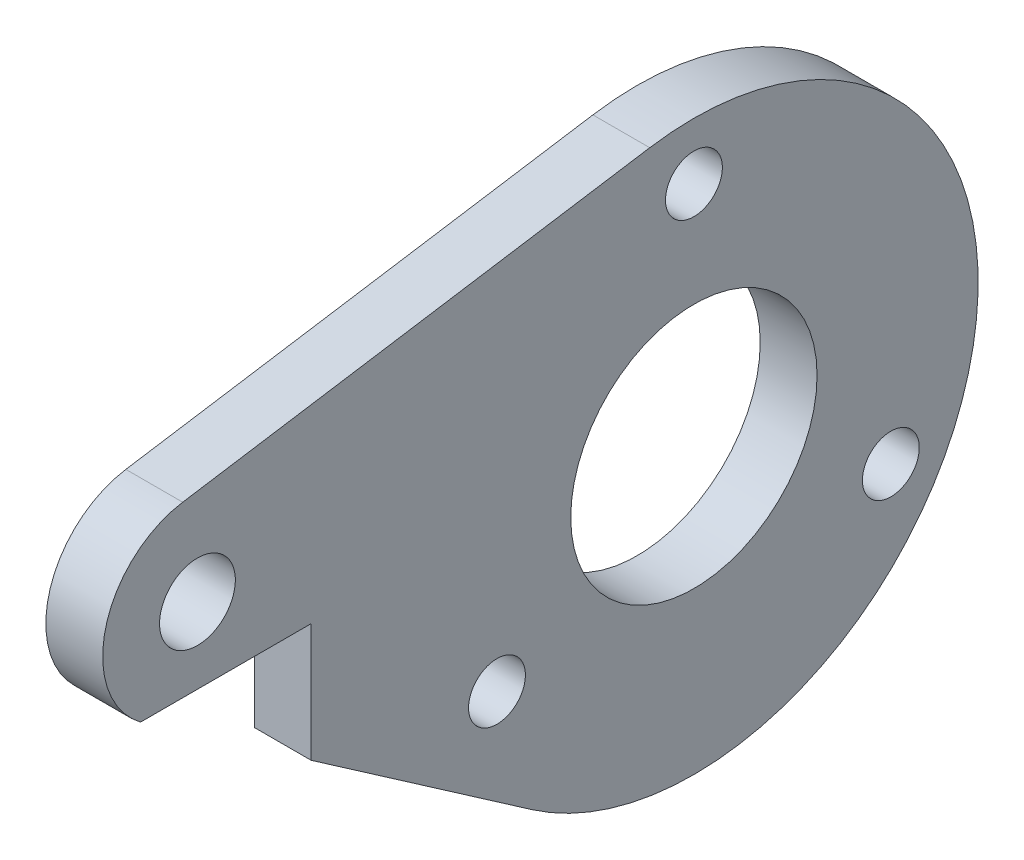
SolidWorks part; units mm, degrees
ref_plane "Plan de face" through (0, 0, 0) normal (0, 0, 1) x (1, 0, 0)
ref_plane "Plan de dessus" through (0, 0, 0) normal (0, 1, 0) x (1, 0, 0)
ref_plane "Plan de droite" through (0, 0, 0) normal (1, 0, 0) x (0, 0, -1)
sketch "Esquisse1" plane through (0, 0, 0) normal (-1, 0, 0) x (0, 0, 1)
  line L0 (29.0493, 1.8913) -> (8.548, -12.3261)
  line L1 (2.3318, 14.8176) -> (26.9773, 10.9392)
  arc A0 (8.548, -12.3261) -> (2.3318, 14.8176) centre (0, 0) cw
  arc A1 (26.9773, 10.9392) -> (29.0493, 1.8913) centre (26.2, 6) cw
  circle A2 centre (0, 0) radius 6.5 construction
  circle A3 centre (0, 0) radius 6.5
  circle A4 centre (-10.3923, -6) radius 1.5
  circle A5 centre (0, 12) radius 1.5
  circle A6 centre (10.3923, -6) radius 1.5
  circle A7 centre (0, 0) radius 15 construction
  circle A8 centre (26.2, 6) radius 2
  circle A9 centre (-10.3923, -6) radius 1.25 construction
  dimension "D1" = 3
  dimension "D2" = 4
  dimension "D3" = 5
extrude "Boss.-Extru.1" add sketch "Esquisse1" against normal blind 3
sketch "Esquisse2" plane through (3, 0, 0) normal (1, 0, 0) x (0, 0, -1)
  line L0 (-29.2061, 2) -> (-20.2, 2)
  line L1 (-8.548, -12.3261) -> (-29.0493, 1.8913) construction
  line L2 (-20.2, 2) -> (-20.2, -4.2456)
  line L3 (-20.2, -4.2456) -> (-29.2061, 2)
  line L6 (-21.2, 1) -> (-31.2, 1) construction
  line L7 (-21.2, -9) -> (-21.2, 1) construction
  dimension "D1" = 1
  dimension "D2" = 1
extrude "Enlèv. mat.-Extru.1" cut sketch "Esquisse2" against normal through all
